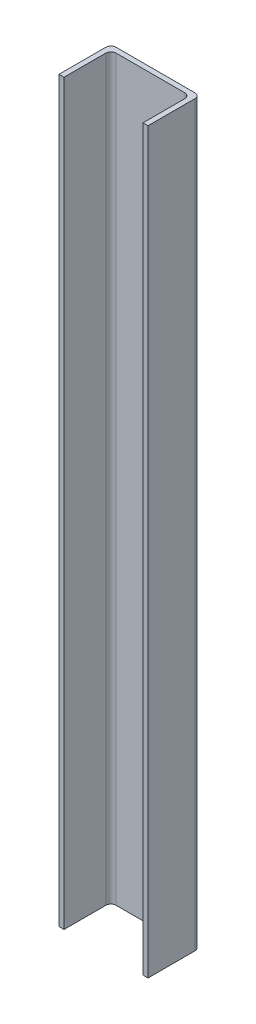
SolidWorks part; units mm, degrees
ref_plane "Front Plane" through (0, 0, 0) normal (0, 0, 1) x (1, 0, 0)
ref_plane "Top Plane" through (0, 0, 0) normal (0, 1, 0) x (1, 0, 0)
ref_plane "Right Plane" through (0, 0, 0) normal (1, 0, 0) x (0, 0, -1)
sketch "Sketch1" plane through (0, 0, 0) normal (0, 1, 0) x (1, 0, 0)
  line L0 (-38.1, -22.225) -> (-33.782, -22.225)
  line L1 (-33.782, 22.225) -> (33.782, 22.225)
  line L2 (-38.1, 17.907) -> (-38.1, -22.225)
  line L4 (38.1, 17.907) -> (38.1, -22.225)
  line L5 (-38.1, 22.225) -> (38.1, -22.225) construction
  line L6 (-38.1, -22.225) -> (38.1, 22.225) construction
  line L7 (-33.782, -22.225) -> (-33.782, 13.589)
  line L8 (-29.464, 17.907) -> (29.464, 17.907)
  line L9 (33.782, 13.589) -> (33.782, -22.225)
  line L10 (33.782, -22.225) -> (38.1, -22.225)
  arc A0 (29.464, 17.907) -> (33.782, 13.589) centre (29.464, 13.589) cw
  arc A1 (-33.782, 13.589) -> (-29.464, 17.907) centre (-29.464, 13.589) cw
  arc A2 (33.782, 22.225) -> (38.1, 17.907) centre (33.782, 17.907) cw
  arc A3 (-33.782, 22.225) -> (-38.1, 17.907) centre (-33.782, 17.907) ccw
  point P0 (0, 0)
  dimension "D6" = 4.318
  dimension "D7" = 4.318
  dimension "D1" = 44.45
  dimension "D2" = 76.2
  dimension "D3" = 4.318
  dimension "D4" = 4.318
  dimension "D5" = 4.318
  dimension "D8" = 40.132
extrude "Boss-Extrude1" add sketch "Sketch1" along normal blind 631.317
